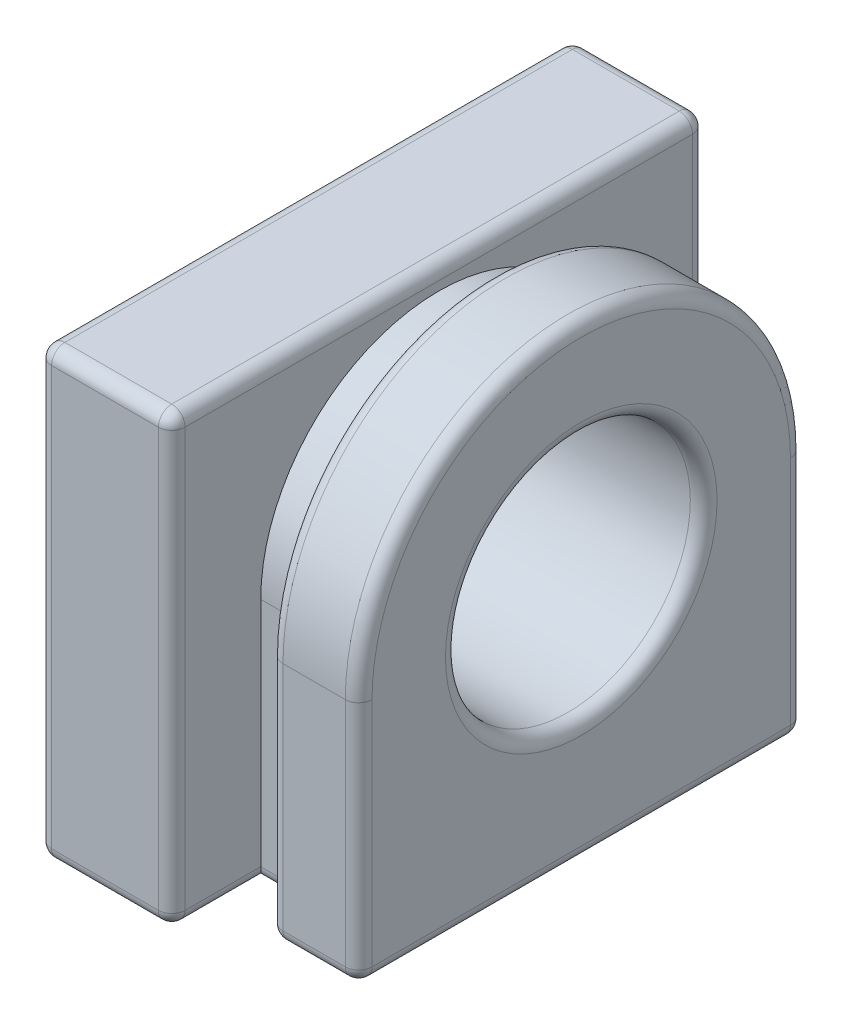
SolidWorks part; units mm, degrees
ref_plane "Front Plane" through (0, 0, 0) normal (0, 0, 1) x (1, 0, 0)
ref_plane "Top Plane" through (0, 0, 0) normal (0, 1, 0) x (1, 0, 0)
ref_plane "Right Plane" through (0, 0, 0) normal (1, 0, 0) x (0, 0, -1)
sketch "Sketch1" plane through (0, 0, 0) normal (1, 0, 0) x (0, 0, -1)
  line L1 (-4, 0) -> (4, 0) construction
  line L2 (-4, 0) -> (-4, -5.5) construction
  line L3 (-4, -5.5) -> (4, -5.5) construction
  line L4 (4, 0) -> (4, -5.5) construction
  line L6 (-4, 0) -> (-4, -5.5)
  line L7 (-4, -5.5) -> (4, -5.5)
  line L8 (4, 0) -> (4, -5.5)
  circle A0 centre (0, 0) radius 4 construction
  arc A1 (4, 0) -> (-4, 0) centre (0, 0) ccw
  dimension "D1" = 8
  dimension "D2" = 5.5
extrude "Boss-Extrude1" add sketch "Sketch1" along normal blind 1.2
sketch "Sketch2" plane through (0, 0, 0) normal (-1, 0, 0) x (0, 0, 1)
  line L0 (0, -5.5) -> (0, 4) construction
  line L1 (4, -5.5) -> (-4, -5.5) construction
  line L3 (-6, -5.5) -> (6, -5.5)
  line L4 (-6, -5.5) -> (-6, 4.5)
  line L5 (-6, 4.5) -> (6, 4.5)
  line L6 (6, -5.5) -> (6, 4.5)
  arc A0 (4, 0) -> (-4, 0) centre (0, 0) ccw construction
  point P11 (0, -5.5)
  dimension "D1" = 12
  dimension "D2" = 0.5
extrude "Boss-Extrude2" add sketch "Sketch2" along normal blind 3
sketch "Sketch3" plane through (1.2, 0, 0) normal (1, 0, 0) x (0, 0, -1)
  line L1 (-5, 0) -> (5, 0) construction
  line L2 (-5, 0) -> (-5, -5.5) construction
  line L3 (-5, -5.5) -> (5, -5.5) construction
  line L4 (5, 0) -> (5, -5.5) construction
  line L5 (-4, -5.5) -> (-6, -5.5) construction
  line L8 (-5, 0) -> (-5, -5.5)
  line L9 (-5, -5.5) -> (5, -5.5)
  line L10 (5, 0) -> (5, -5.5)
  circle A0 centre (0, 0) radius 5 construction
  arc A1 (5, 0) -> (-5, 0) centre (0, 0) ccw
  dimension "D1" = 10
extrude "Boss-Extrude3" add sketch "Sketch3" along normal blind 2
sketch "Sketch4" plane through (3.2, 0, 0) normal (1, 0, 0) x (0, 0, -1)
  circle A0 centre (0, 0) radius 2.75
  dimension "D1" = 5.5
extrude "Cut-Extrude1" cut sketch "Sketch4" against normal up to next
fillet "Fillet1" radius 0.3 28 edges at (1.2, -2.75, -5) (1.2, -2.75, 5) (3.2, -2.75, -5) (3.2, -2.75, 5) (-3, 0, -2.75) (-3, 4.5, 0) (-1.5, 4.5, -6) (-3, -0.5, -6) (0, -0.5, -6) (-1.5, -5.5, -6) (-3, -5.5, 0) (-3, -0.5, 6) (0, 4.5, 0) (-1.5, 4.5, 6) (0, -0.5, 6) (-1.5, -5.5, 6) (2.2, -5.5, -5) (2.2, -5.5, 5) (1.2, 5, 0) (3.2, 0, -2.75) (3.2, -5.5, 0) (3.2, 5, 0)
